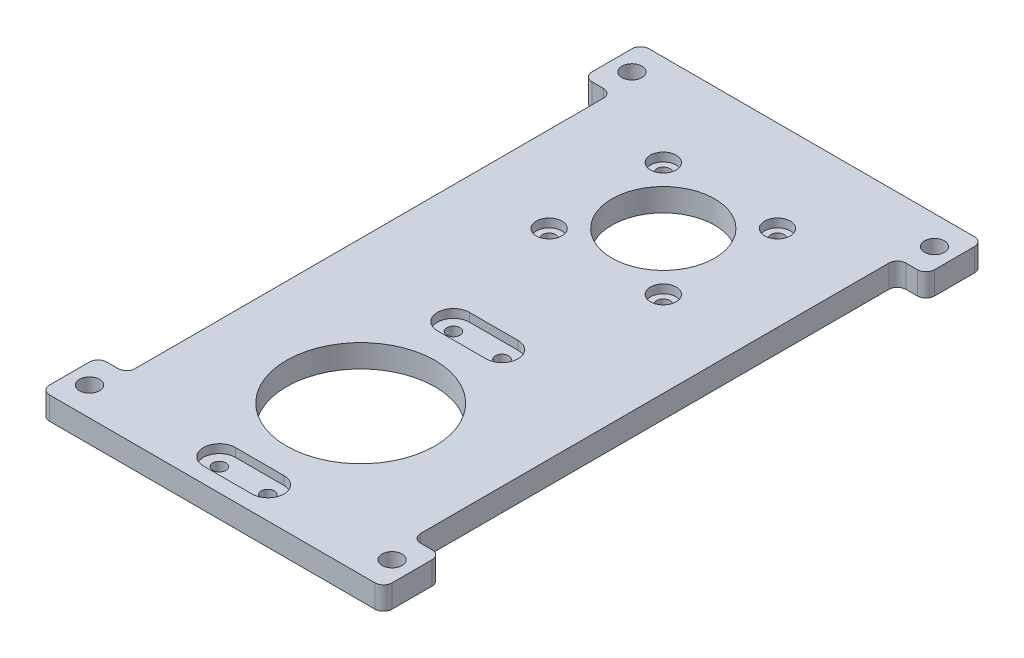
SolidWorks part; units mm, degrees
ref_plane "前视基准面" through (0, 0, 0) normal (0, 0, 1) x (1, 0, 0)
ref_plane "上视基准面" through (0, 0, 0) normal (0, 1, 0) x (1, 0, 0)
ref_plane "右视基准面" through (0, 0, 0) normal (1, 0, 0) x (0, 0, -1)
other "Configuration Table"
sketch "草图1" plane through (0, 0, 0) normal (0, 1, 0) x (1, 0, 0)
  line L0 (51.4316, 41.9478) -> (101.4316, 41.9478)
  line L1 (101.4316, 41.9478) -> (101.4316, 146.9478)
  line L2 (101.4316, 146.9478) -> (51.4316, 146.9478)
  line L3 (51.4316, 146.9478) -> (51.4316, 41.9478)
extrude "凸台-拉伸1" add sketch "草图1" along normal blind 4
sketch "草图2" plane through (0, 4, 0) normal (0, 1, 0) x (1, 0, 0)
  circle A0 centre (72.1816, 88.4478) radius 1.15
  circle A1 centre (72.1816, 47.4478) radius 1.15
  circle A2 centre (80.6816, 47.4478) radius 1.15
  circle A3 centre (80.6816, 88.4478) radius 1.15
extrude "切除-拉伸1" cut sketch "草图2" against normal blind 5
sketch "草图3" plane through (0, 4, 0) normal (0, 1, 0) x (1, 0, 0)
  line L0 (72.1816, 91.2478) -> (80.6816, 91.2478)
  line L1 (80.6816, 85.6478) -> (72.1816, 85.6478)
  line L2 (80.6816, 44.6478) -> (72.1816, 44.6478)
  line L3 (72.1816, 50.2478) -> (80.6816, 50.2478)
  arc A0 (80.6816, 85.6478) -> (80.6816, 91.2478) centre (80.6816, 88.4478) ccw
  arc A1 (72.1816, 91.2478) -> (72.1816, 85.6478) centre (72.1816, 88.4478) ccw
  arc A2 (80.6816, 44.6478) -> (80.6816, 50.2478) centre (80.6816, 47.4478) ccw
  arc A3 (72.1816, 50.2478) -> (72.1816, 44.6478) centre (72.1816, 47.4478) ccw
extrude "切除-拉伸2" cut sketch "草图3" against normal blind 1.5
sketch "草图4" plane through (0, 4, 0) normal (0, 1, 0) x (1, 0, 0)
  circle A0 centre (86.4316, 130.9478) radius 2.25
  circle A1 centre (86.4316, 110.9478) radius 2.25
  circle A2 centre (66.4316, 110.9478) radius 2.25
  circle A3 centre (66.4316, 130.9478) radius 2.25
extrude "切除-拉伸3" cut sketch "草图4" against normal blind 1.5
sketch "草图5" plane through (0, 2.5, 0) normal (0, 1, 0) x (1, 0, 0)
  circle A0 centre (66.4316, 130.9478) radius 1.15
  circle A1 centre (86.4316, 130.9478) radius 1.15
  circle A2 centre (66.4316, 110.9478) radius 1.15
  circle A3 centre (86.4316, 110.9478) radius 1.15
extrude "切除-拉伸4" cut sketch "草图5" against normal through all
sketch "草图6" plane through (0, 4, 0) normal (0, 1, 0) x (1, 0, 0)
  line L0 (101.4316, 41.9478) -> (101.4316, 51.9478)
  line L1 (101.4316, 41.9478) -> (101.4316, 146.9478) construction
  line L2 (101.4316, 41.9478) -> (106.4316, 41.9478)
  line L3 (106.4316, 41.9478) -> (106.4316, 51.9478)
  line L4 (106.4316, 51.9478) -> (101.4316, 51.9478)
  line L5 (51.4316, 41.9478) -> (46.4316, 41.9478)
  line L6 (46.4316, 41.9478) -> (46.4316, 51.9478)
  line L7 (46.4316, 51.9478) -> (51.4316, 51.9478)
  line L8 (51.4316, 146.9478) -> (51.4316, 41.9478) construction
  line L9 (51.4316, 51.9478) -> (51.4316, 41.9478)
  line L11 (51.4316, 136.9478) -> (51.4316, 146.9478)
  line L12 (46.4316, 136.9478) -> (51.4316, 136.9478)
  line L13 (46.4316, 146.9478) -> (46.4316, 136.9478)
  line L14 (51.4316, 146.9478) -> (46.4316, 146.9478)
  line L15 (106.4316, 136.9478) -> (101.4316, 136.9478)
  line L16 (106.4316, 146.9478) -> (106.4316, 136.9478)
  line L17 (101.4316, 146.9478) -> (106.4316, 146.9478)
  line L18 (101.4316, 146.9478) -> (101.4316, 136.9478)
extrude "凸台-拉伸2" add sketch "草图6" against normal up to surface (4 mm away) up to face at (86.4316, 0, -129.7978)
sketch "草图7" plane through (0, 4, 0) normal (0, 1, 0) x (1, 0, 0)
  circle A0 centre (102.9316, 46.9478) radius 1.75
  circle A1 centre (49.9316, 46.9478) radius 1.75
  circle A2 centre (49.9316, 141.9478) radius 1.75
  circle A3 centre (102.9316, 141.9478) radius 1.75
extrude "切除-拉伸5" cut sketch "草图7" against normal through all
sketch "草图8" plane through (0, 4, 0) normal (0, 1, 0) x (1, 0, 0)
  circle A0 centre (76.4316, 67.9478) radius 13
  circle A1 centre (76.4316, 120.9478) radius 9
extrude "切除-拉伸6" cut sketch "草图8" against normal through all
fillet "圆角1" radius 1.5 12 edges at (101.4316, 2, -136.9478) (106.4316, 2, -136.9478) (106.4316, 2, -146.9478) (106.4316, 2, -41.9478) (106.4316, 2, -51.9478) (101.4316, 2, -51.9478) (51.4316, 2, -51.9478) (46.4316, 2, -41.9478) (46.4316, 2, -51.9478) (51.4316, 2, -136.9478) (46.4316, 2, -146.9478) (46.4316, 2, -136.9478)
